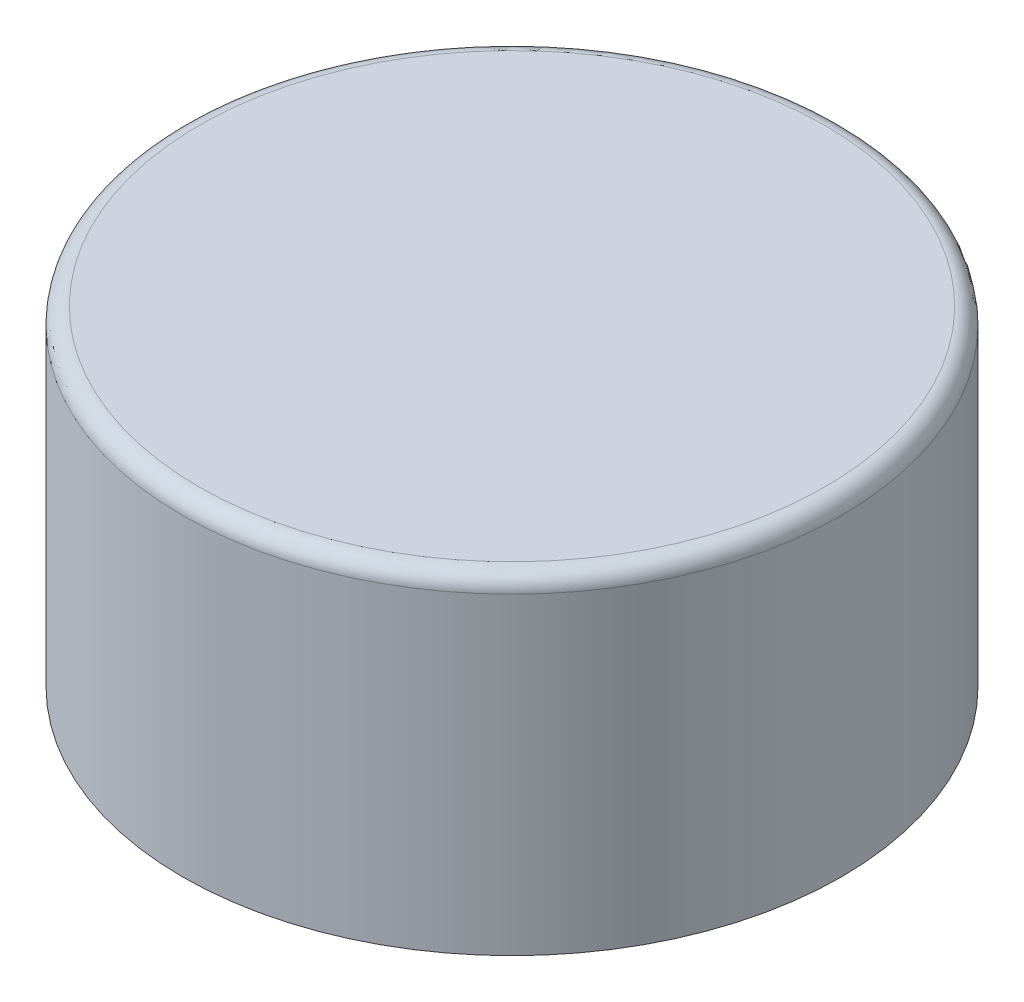
SolidWorks part; units mm, degrees
material "Ge"
ref_plane "前视基准面" through (0, 0, 0) normal (0, 0, 1) x (1, 0, 0)
ref_plane "上视基准面" through (0, 0, 0) normal (0, 1, 0) x (1, 0, 0)
ref_plane "右视基准面" through (0, 0, 0) normal (1, 0, 0) x (0, 0, -1)
sketch "草图1" plane through (0, 0, 0) normal (0, 1, 0) x (1, 0, 0)
  circle A0 centre (0, 0) radius 40
extrude "凸台-拉伸1" add sketch "草图1" along normal blind 40
fillet "圆角1" radius 2 1 edges at (0, 40, 40)
sketch "草图2" plane through (0, 0, 0) normal (0, 0, 1) x (1, 0, 0)
  line L1 (0, 0) -> (0.5, 0)
  line L6 (0, 0) -> (0, 1)
  line L7 (0, 1) -> (0.5, 1)
  line L8 (0.5, 0) -> (0.5, 1)
  line L9 (0, 0) -> (0.5, 1) construction
  line L10 (0, 1) -> (0.5, 0) construction
  point P4 (0.25, 0.5)
sketch "草图3" plane through (0, 0, 0) normal (0, -1, 0) x (1, 0, 0)
  circle A0 centre (0, 0) radius 9
sweep "切除-扫描3" cut path "草图3" circular profile diameter 1.5 parameters "D3"=1.5
revolve "切除-旋转1" cut sketch "草图2" angle 360 about L6
